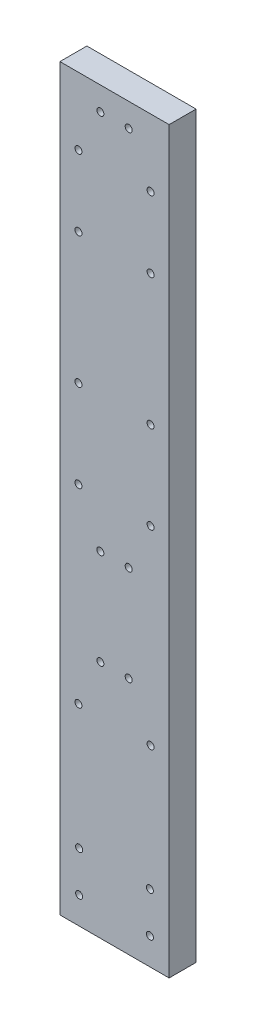
SolidWorks part; units mm, degrees
ref_plane "Front Plane" through (0, 0, 0) normal (0, 0, 1) x (1, 0, 0)
ref_plane "Top Plane" through (0, 0, 0) normal (0, 1, 0) x (1, 0, 0)
ref_plane "Right Plane" through (0, 0, 0) normal (1, 0, 0) x (0, 0, -1)
sketch "Sketch1" plane through (0, 0, 0) normal (0, 0, 1) x (1, 0, 0)
  line L0 (16.2, 0) -> (16.2, 109.64)
  line L1 (16.2, 109.64) -> (0, 109.64)
  line L2 (0, 109.64) -> (0, 0)
  line L3 (0, 0) -> (16.2, 0)
  line L4 (16.2, 59.21) -> (0, 59.21) construction
  line L5 (0, 14) -> (16.2, 14) construction
  line L6 (0, 26) -> (16.2, 26) construction
  line L7 (0, 91.66) -> (16.2, 91.66) construction
  line L8 (0, 67.21) -> (16.2, 67.21) construction
  line L9 (8.1, 109.64) -> (8.1, 97.66) construction
  line L11 (0, 97.66) -> (16.2, 97.66) construction
  circle A0 centre (13.45, 56.71) radius 0.52
  circle A1 centre (10.2, 49.71) radius 0.52
  circle A2 centre (10.2, 106.16) radius 0.52
  circle A3 centre (2.75, 99.66) radius 0.52
  circle A4 centre (6, 49.71) radius 0.52
  circle A5 centre (2.75, 28.5) radius 0.52
  circle A6 centre (2.75, 89.16) radius 0.52
  circle A7 centre (2.75, 56.71) radius 0.52
  circle A8 centre (13.45, 89.16) radius 0.52
  circle A9 centre (13.45, 99.66) radius 0.52
  circle A28 centre (13.45, 69.71) radius 0.52
  circle A29 centre (6, 35.5) radius 0.52
  circle A32 centre (6, 106.16) radius 0.52
  circle A33 centre (10.2, 35.5) radius 0.52
  circle A34 centre (2.75, 69.71) radius 0.52
  circle A35 centre (13.45, 28.5) radius 0.52
  circle A36 centre (2.85, 10) radius 0.52
  circle A37 centre (13.35, 10) radius 0.52
  circle A38 centre (13.35, 4) radius 0.52
  circle A39 centre (2.85, 4) radius 0.52
  dimension "D1" = 4
  dimension "D2" = 4
  dimension "D3" = 2.85
  dimension "D4" = 2.85
  dimension "D5" = 16.2
  dimension "D6" = 6
  dimension "D7" = 6
  dimension "D8" = 2.85
  dimension "D9" = 2.85
  dimension "D10" = 4
  dimension "D11" = 12
  dimension "D12" = 33.21
  dimension "D13" = 2.5
  dimension "D14" = 2.5
  dimension "D15" = 2.75
  dimension "D16" = 2.75
  dimension "D17" = 2.5
  dimension "D18" = 2.5
  dimension "D19" = 2.75
  dimension "D20" = 2.75
  dimension "D21" = 9.5
  dimension "D22" = 6
  dimension "D23" = 9.5
  dimension "D24" = 6
  dimension "D25" = 9.5
  dimension "D26" = 9.5
  dimension "D27" = 6
  dimension "D28" = 6
  dimension "D29" = 8
  dimension "D30" = 24.45
  dimension "D31" = 2.5
  dimension "D32" = 2.5
  dimension "D33" = 2.75
  dimension "D34" = 2.75
  dimension "D35" = 6
  dimension "D36" = 2.75
  dimension "D37" = 2
  dimension "D38" = 6
  dimension "D39" = 8.5
  dimension "D40" = 11.98
  dimension "D41" = 2.5
  dimension "D42" = 2.5
  dimension "D43" = 2.75
  dimension "D44" = 2.75
extrude "Boss-Extrude1" add sketch "Sketch1" along normal blind 4
equation "\"D12@Sketch1\"= \"HL@parametersSketch@prostheticParameters.SLDPRT\" * 0.266 - 12 - 4 'Middle PIP Length"
equation "\"D30@Sketch1\"= \"HL@parametersSketch@prostheticParameters.SLDPRT\" * 0.17 - 4 - 3'Middle MIP Length"
equation "\"D5@Sketch1\"= \"fingerWidth@parametersSketch@prostheticParameters.SLDPRT\" 'Middle Width"
equation "\"D40@Sketch1\"= \"HL@parametersSketch@prostheticParameters.SLDPRT\" * 0.108 - 3 - 5'Middle DIP Length"
